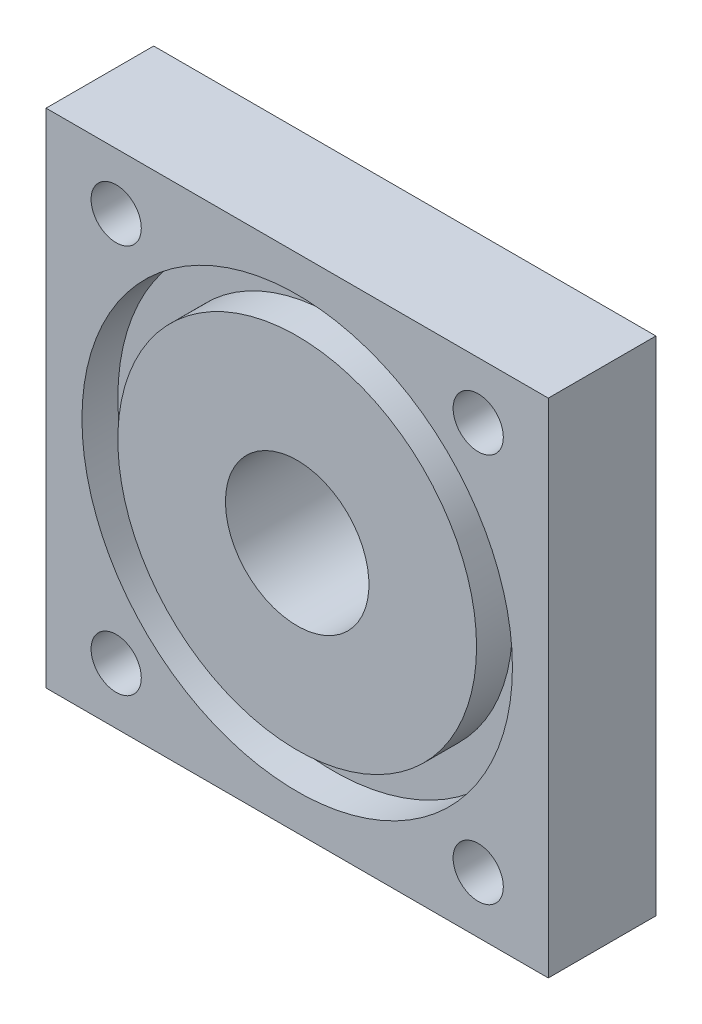
SolidWorks part; units mm, degrees
ref_plane "Front Plane" through (0, 0, 0) normal (0, 0, 1) x (1, 0, 0)
ref_plane "Top Plane" through (0, 0, 0) normal (0, 1, 0) x (1, 0, 0)
ref_plane "Right Plane" through (0, 0, 0) normal (1, 0, 0) x (0, 0, -1)
sketch "Sketch1" plane through (0, 0, 0) normal (0, 0, 1) x (1, 0, 0)
  line L1 (-35, -35) -> (35, -35)
  line L2 (-35, -35) -> (-35, 35)
  line L3 (-35, 35) -> (35, 35)
  line L4 (35, -35) -> (35, 35)
  line L5 (-35, -35) -> (35, 35) construction
  line L6 (-35, 35) -> (35, -35) construction
  point P0 (0, 0)
  dimension "D1" = 70
  dimension "D2" = 70
extrude "Boss-Extrude1" add sketch "Sketch1" along normal blind 15
sketch "Sketch2" plane through (0, 0, 15) normal (0, 0, 1) x (1, 0, 0)
  line L1 (-25.2299, -27.138) -> (25.2299, -27.138) construction
  line L2 (-25.2299, -27.138) -> (-25.2299, 27.138) construction
  line L3 (-25.2299, 27.138) -> (25.2299, 27.138) construction
  line L4 (25.2299, -27.138) -> (25.2299, 27.138) construction
  line L5 (-25.2299, -27.138) -> (25.2299, 27.138) construction
  line L6 (-25.2299, 27.138) -> (25.2299, -27.138) construction
  circle A0 centre (0, 0) radius 25
  circle A1 centre (0, 0) radius 30
  circle A2 centre (0, -0.6056) radius 37.5 construction
  circle A3 centre (-25.2299, 27.138) radius 3.5
  circle A4 centre (25.2299, 27.138) radius 3.5
  circle A5 centre (25.2299, -27.138) radius 3.5
  circle A6 centre (-25.2299, -27.138) radius 3.5
  dimension "D1" = 50
  dimension "D2" = 60
  dimension "D3" = 75
  dimension "D4" = 7
  dimension "D5" = 7
  dimension "D6" = 7
  dimension "D7" = 7
extrude "Cut-Extrude1" cut sketch "Sketch2" against normal blind 5
sketch "Sketch3" plane through (0, 0, 0) normal (0, 0, 1) x (1, 0, 0)
  circle A0 centre (-25.2299, 27.138) radius 3.5
  circle A1 centre (25.2299, 27.138) radius 3.5
  circle A2 centre (25.2299, -27.138) radius 3.5
  circle A3 centre (-25.2299, -27.138) radius 3.5
extrude "Cut-Extrude2" cut sketch "Sketch3" along normal through all
sketch "Sketch4" plane through (0, 0, 0) normal (0, 0, -1) x (-1, 0, 0)
  circle A0 centre (0, 0) radius 10
  dimension "D1" = 20
extrude "Cut-Extrude3" cut sketch "Sketch4" against normal through all
